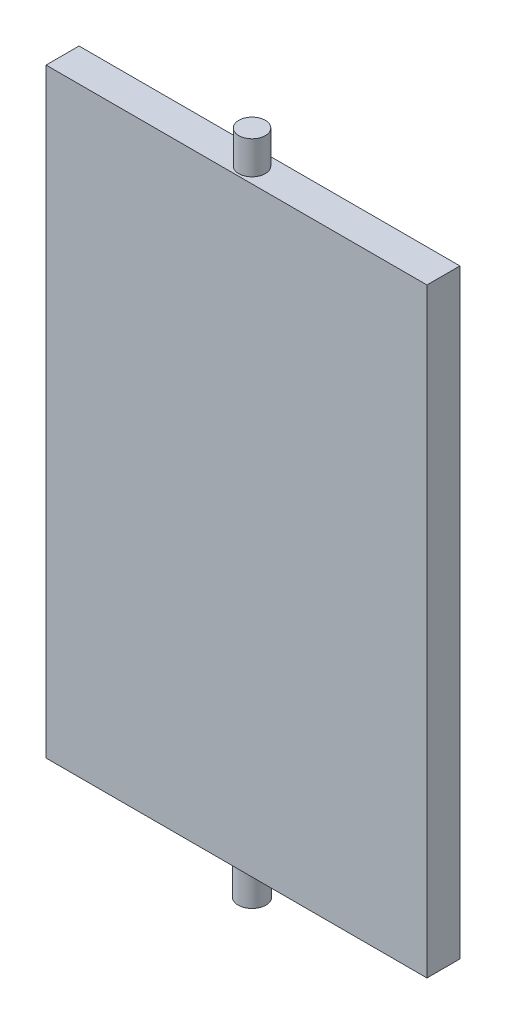
SolidWorks part; units mm, degrees
ref_plane "Front Plane" through (0, 0, 0) normal (0, 0, 1) x (1, 0, 0)
ref_plane "Top Plane" through (0, 0, 0) normal (0, 1, 0) x (1, 0, 0)
ref_plane "Right Plane" through (0, 0, 0) normal (1, 0, 0) x (0, 0, -1)
sketch "Sketch1" plane through (0, 0, 0) normal (0, 0, 1) x (1, 0, 0)
  line L0 (-26.771, 18.7739) -> (214.229, 18.7739)
  line L1 (214.229, 18.7739) -> (214.229, -355.2261)
  line L2 (214.229, -355.2261) -> (-26.771, -355.2261)
  line L3 (-26.771, -355.2261) -> (-26.771, 18.7739)
extrude "Boss-Extrude1" add sketch "Sketch1" along normal blind 20
sketch "Sketch5" plane through (0, -355.2261, 0) normal (0, -1, 0) x (1, 0, 0)
  line L0 (214.229, 0) -> (93.729, 0)
  line L1 (-26.771, 0) -> (214.229, 0) construction
  circle A0 centre (93.729, 10.5776) radius 8.426
extrude "Boss-Extrude3" add sketch "Sketch5" along normal blind 20 contours A0
sketch "Sketch6" plane through (0, 18.7739, 0) normal (0, 1, 0) x (1, 0, 0)
  line L1 (-26.771, 0) -> (214.229, 0)
  line L2 (-26.771, 0) -> (-26.771, -20)
  line L3 (-26.771, -20) -> (214.229, -20)
  line L4 (214.229, 0) -> (214.229, -20)
extrude "Cut-Extrude1" cut sketch "Sketch6" against normal blind 5
sketch "Sketch7" plane through (0, 13.7739, 0) normal (0, 1, 0) x (1, 0, 0)
  line L0 (214.229, -20) -> (93.729, -20)
  line L1 (-26.771, -20) -> (214.229, -20) construction
  circle A0 centre (93.729, -10.4868) radius 8.4048
extrude "Boss-Extrude4" add sketch "Sketch7" along normal blind 20 contours A0
sketch "Sketch8" plane through (-26.771, 0, 0) normal (-1, 0, 0) x (0, 0, 1)
  line L0 (0, 13.7739) -> (20, 13.7739)
  line L1 (20, 13.7739) -> (20, -355.2261)
  line L2 (20, -355.2261) -> (0, -355.2261)
  line L3 (0, -355.2261) -> (0, 13.7739)
extrude "Cut-Extrude2" cut sketch "Sketch8" against normal blind 5
sketch "Sketch9" plane through (214.229, 0, 0) normal (1, 0, 0) x (0, 0, -1)
  line L0 (-20, 13.7739) -> (0, 13.7739)
  line L1 (0, 13.7739) -> (0, -355.2261)
  line L2 (0, -355.2261) -> (-20, -355.2261)
  line L3 (-20, -355.2261) -> (-20, 13.7739)
extrude "Cut-Extrude3" cut sketch "Sketch9" against normal blind 5
sketch "Sketch11" plane through (0, -375.2261, 0) normal (0, -1, 0) x (1, 0, 0)
  circle A0 centre (93.729, 10.5776) radius 8.426
extrude "Cut-Extrude4" cut sketch "Sketch11" against normal blind 10
sketch "Sketch12" plane through (0, 33.7739, 0) normal (0, 1, 0) x (1, 0, 0)
  circle A0 centre (93.729, -10.4868) radius 8.4048
extrude "Cut-Extrude5" cut sketch "Sketch12" against normal blind 10
sketch "Sketch13" plane through (0, 23.7739, 0) normal (0, 1, 0) x (1, 0, 0)
  circle A0 centre (93.729, -10.4868) radius 8.4048
extrude "Boss-Extrude6" add sketch "Sketch13" along normal blind 10
sketch "Sketch14" plane through (0, -365.2261, 0) normal (0, -1, 0) x (1, 0, 0)
  circle A0 centre (93.729, 10.5776) radius 8.426
extrude "Boss-Extrude7" add sketch "Sketch14" along normal blind 10
sketch "Sketch15" plane through (0, 13.7739, 0) normal (0, 1, 0) x (1, 0, 0)
  line L1 (-21.771, 0) -> (209.229, 0)
  line L2 (-21.771, 0) -> (-21.771, -20)
  line L3 (-21.771, -20) -> (209.229, -20)
  line L4 (209.229, 0) -> (209.229, -20)
extrude "Cut-Extrude6" cut sketch "Sketch15" against normal blind 5
sketch "Sketch16" plane through (0, 8.7739, 0) normal (0, 1, 0) x (1, 0, 0)
  line L0 (209.229, -20) -> (93.729, -20)
  line L1 (-21.771, -20) -> (209.229, -20) construction
  circle A0 centre (93.729, -10.5776) radius 8.05
extrude "Boss-Extrude8" add sketch "Sketch16" along normal blind 20 contours A0
